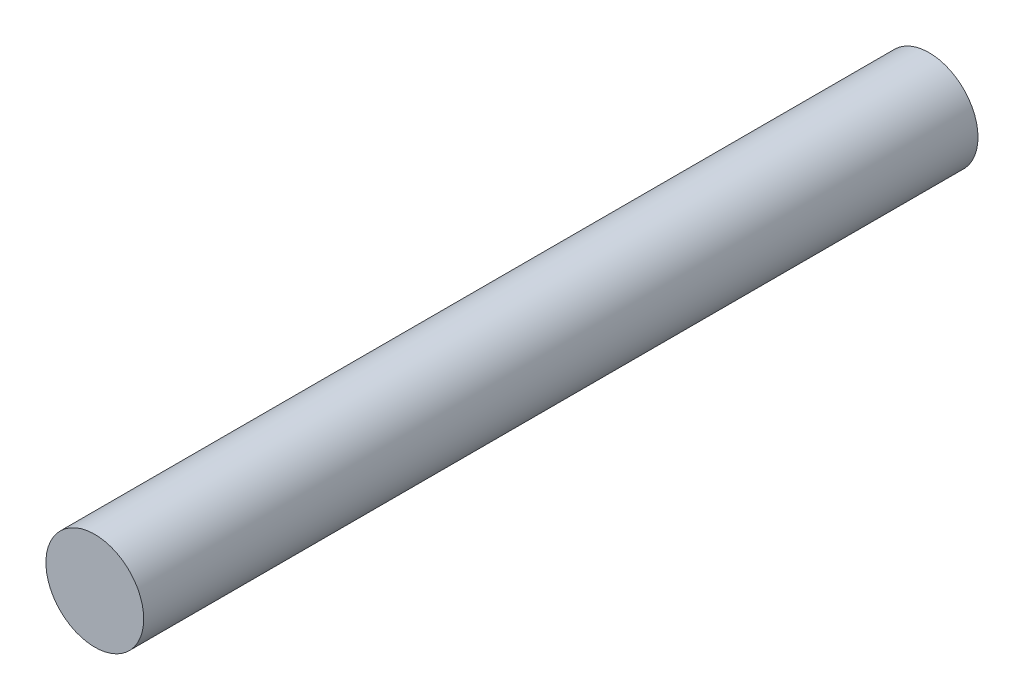
SolidWorks part; units mm, degrees
ref_plane "Front Plane" through (0, 0, 0) normal (0, 0, 1) x (1, 0, 0)
ref_plane "Top Plane" through (0, 0, 0) normal (0, 1, 0) x (1, 0, 0)
ref_plane "Right Plane" through (0, 0, 0) normal (1, 0, 0) x (0, 0, -1)
sketch "Sketch1" plane through (0, 0, 0) normal (0, 0, 1) x (1, 0, 0)
  circle A0 centre (0, 0) radius 2.3813
  dimension "D1" = 4.7625
extrude "Boss-Extrude1" add sketch "Sketch1" along normal blind 40.64
